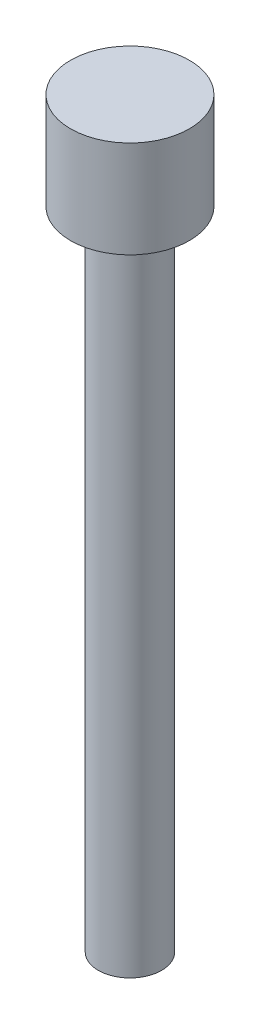
SolidWorks part; units mm, degrees
ref_plane "Front Plane" through (0, 0, 0) normal (0, 0, 1) x (1, 0, 0)
ref_plane "Top Plane" through (0, 0, 0) normal (0, 1, 0) x (1, 0, 0)
ref_plane "Right Plane" through (0, 0, 0) normal (1, 0, 0) x (0, 0, -1)
sketch "Sketch1" plane through (0, 0, 0) normal (0, 1, 0) x (1, 0, 0)
  circle A0 centre (0, 0) radius 1.84
  dimension "D1" = 3.68
extrude "Boss-Extrude1" add sketch "Sketch1" along normal blind 3
sketch "Sketch2" plane through (0, 0, 0) normal (0, -1, 0) x (1, 0, 0)
  circle A0 centre (0, 0) radius 0.98
  dimension "D1" = 1.96
extrude "Boss-Extrude2" add sketch "Sketch2" along normal blind 20
